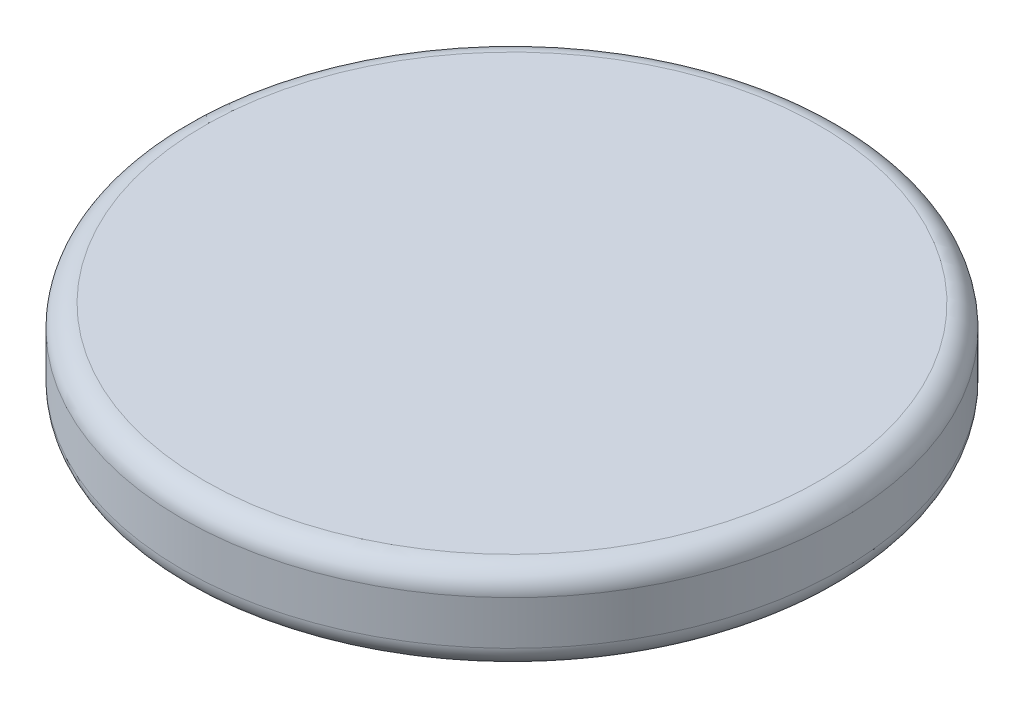
SolidWorks part; units mm, degrees
material "Zinc Alloy 7; AG40B; Zn-4Al-0.015Mg"
ref_plane "Front Plane" through (0, 0, 0) normal (0, 0, 1) x (1, 0, 0)
ref_plane "Top Plane" through (0, 0, 0) normal (0, 1, 0) x (1, 0, 0)
ref_plane "Right Plane" through (0, 0, 0) normal (1, 0, 0) x (0, 0, -1)
sketch "Sketch1" plane through (0, 0, 0) normal (0, 1, 0) x (1, 0, 0)
  circle A0 centre (0, 0) radius 7.5
  dimension "D1" = 15
extrude "Boss-Extrude1" add sketch "Sketch1" along normal blind 2
fillet "Fillet1" radius 0.5 2 edges at (0, 0, 7.5) (0, 2, 7.5)
